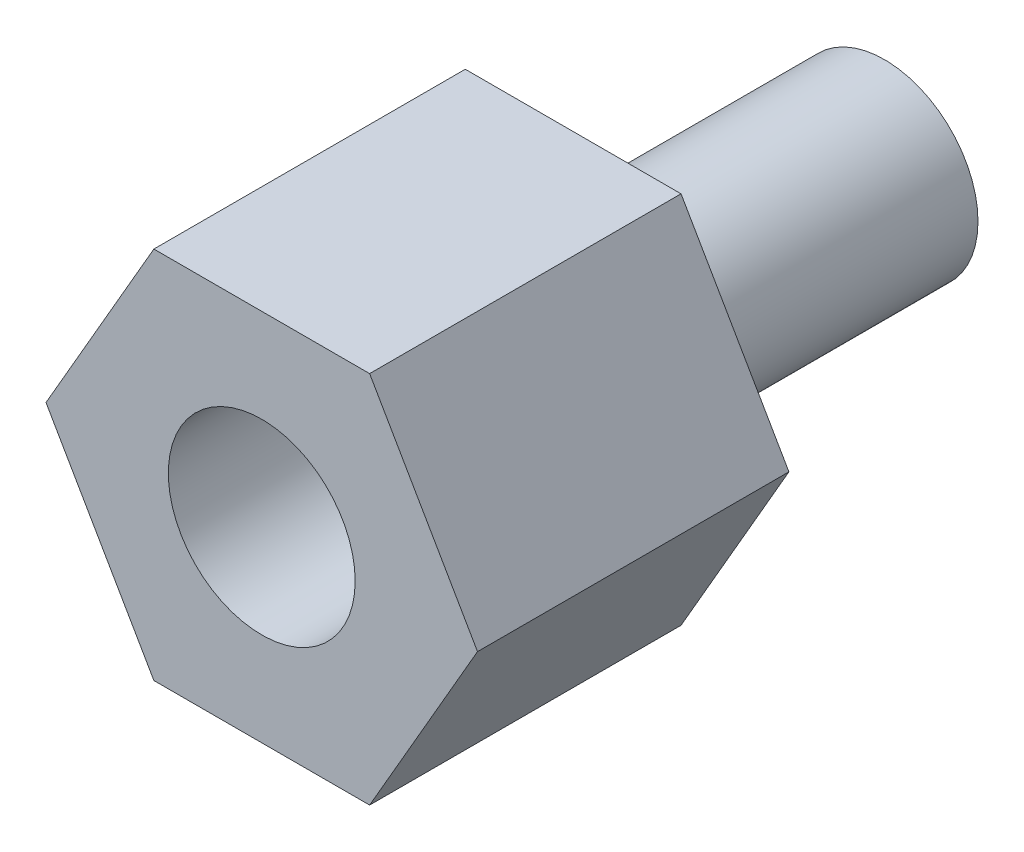
SolidWorks part; units mm, degrees
material "ЛА67-2,5 ГОСТ 15527-70"
ref_plane "Спереди" through (0, 0, 0) normal (0, 0, 1) x (1, 0, 0)
ref_plane "Сверху" through (0, 0, 0) normal (0, 1, 0) x (1, 0, 0)
ref_plane "Справа" through (0, 0, 0) normal (1, 0, 0) x (0, 0, -1)
sketch "Эскиз1" plane through (0, 0, 0) normal (0, 0, 1) x (1, 0, 0)
  circle A0 centre (0, 0) radius 1.5
  dimension "D1" = 3
extrude "Бобышка-Вытянуть1" add sketch "Эскиз1" along normal blind 5
sketch "Эскиз2" plane through (0, 0, 5) normal (0, 0, 1) x (1, 0, 0)
  line L1 (-3.4641, 0) -> (-1.7321, -3)
  line L2 (-1.7321, -3) -> (1.7321, -3)
  line L3 (1.7321, -3) -> (3.4641, 0)
  line L4 (3.4641, 0) -> (1.7321, 3)
  line L5 (1.7321, 3) -> (-1.7321, 3)
  line L6 (-1.7321, 3) -> (-3.4641, 0)
  circle A0 centre (0, 0) radius 3 construction
  dimension "D1" = 3
extrude "Бобышка-Вытянуть2" add sketch "Эскиз2" along normal blind 5
sketch "Эскиз3" plane through (0, 0, 10) normal (0, 0, 1) x (1, 0, 0)
  circle A0 centre (0, 0) radius 1.5
  dimension "D1" = 3
extrude "Вырез-Вытянуть1" cut sketch "Эскиз3" against normal blind 4
